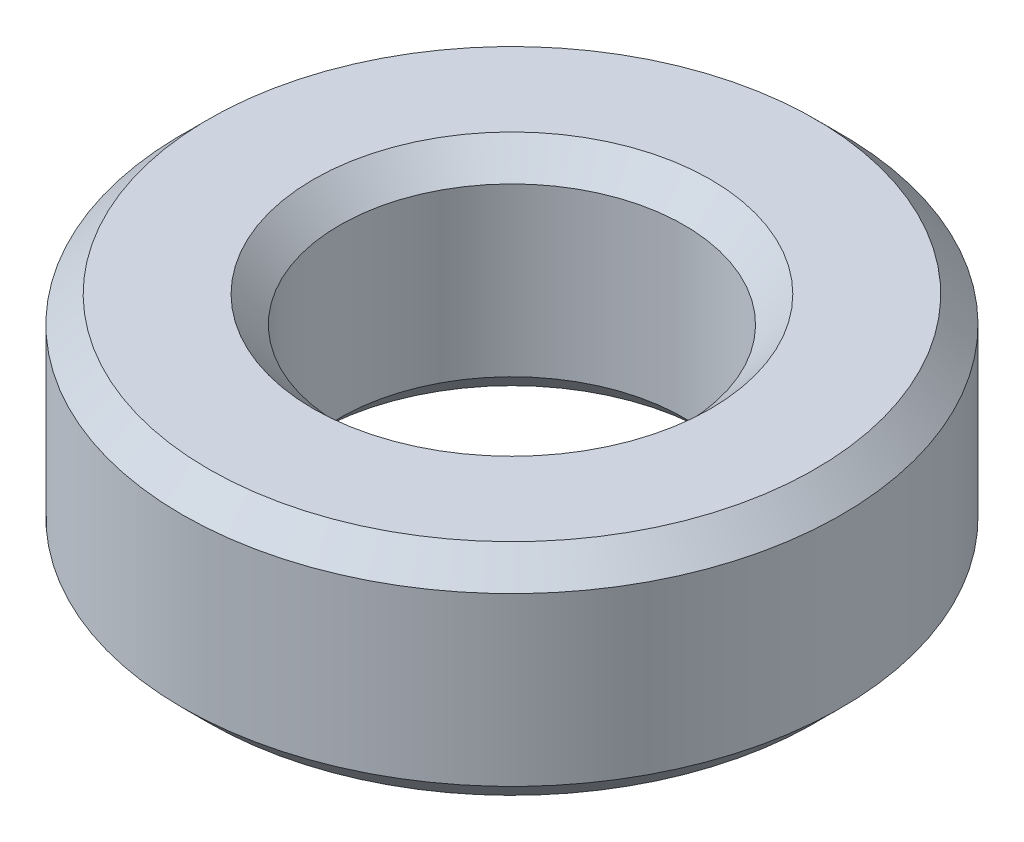
SolidWorks part; units mm, degrees
material "Alum Plate"
ref_plane "Front Plane" through (0, 0, 0) normal (0, 0, 1) x (1, 0, 0)
ref_plane "Top Plane" through (0, 0, 0) normal (0, 1, 0) x (1, 0, 0)
ref_plane "Right Plane" through (0, 0, 0) normal (1, 0, 0) x (0, 0, -1)
other "Bounding Box"
ref_plane "Default Plane" through (-8.9266, -12.7485, 0) normal (-0.1736, 0.9848, 0) x (0.9848, 0.1736, 0)
sketch "Sketch1" plane through (0, 0, 0) normal (0, 1, 0) x (1, 0, 0)
  circle A0 centre (0, 0) radius 2.4892
  circle A1 centre (0, 0) radius 4.7625
  dimension "D1" = 9.525
  dimension "D2" = 4.9784
extrude "Boss-Extrude1" add sketch "Sketch1" along normal mid plane 3.175
chamfer "Chamfer1" distance 0.381 angle 45 4 edges at (0, -1.5875, 2.4892) (0, -1.5875, 4.7625) (0, 1.5875, 2.4892) (0, 1.5875, 4.7625)
